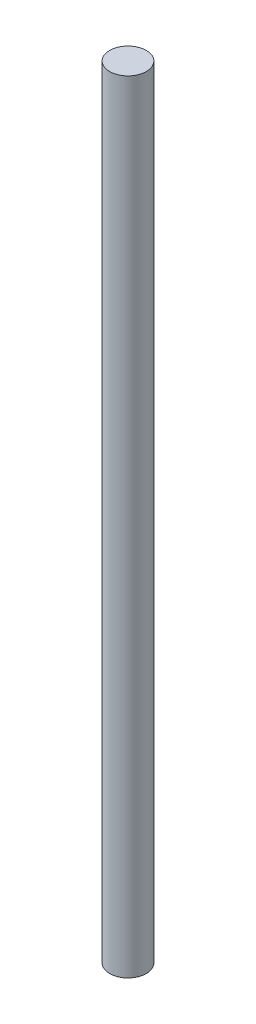
SolidWorks part; units mm, degrees
ref_plane "Front Plane" through (0, 0, 0) normal (0, 0, 1) x (1, 0, 0)
ref_plane "Top Plane" through (0, 0, 0) normal (0, 1, 0) x (1, 0, 0)
ref_plane "Right Plane" through (0, 0, 0) normal (1, 0, 0) x (0, 0, -1)
sketch "Sketch1" plane through (0, 0, 0) normal (0, 1, 0) x (1, 0, 0)
  circle A0 centre (0, 0) radius 4.7625
  dimension "D1" = 9.525
extrude "Boss-Extrude1" add sketch "Sketch1" along normal blind 203.2
